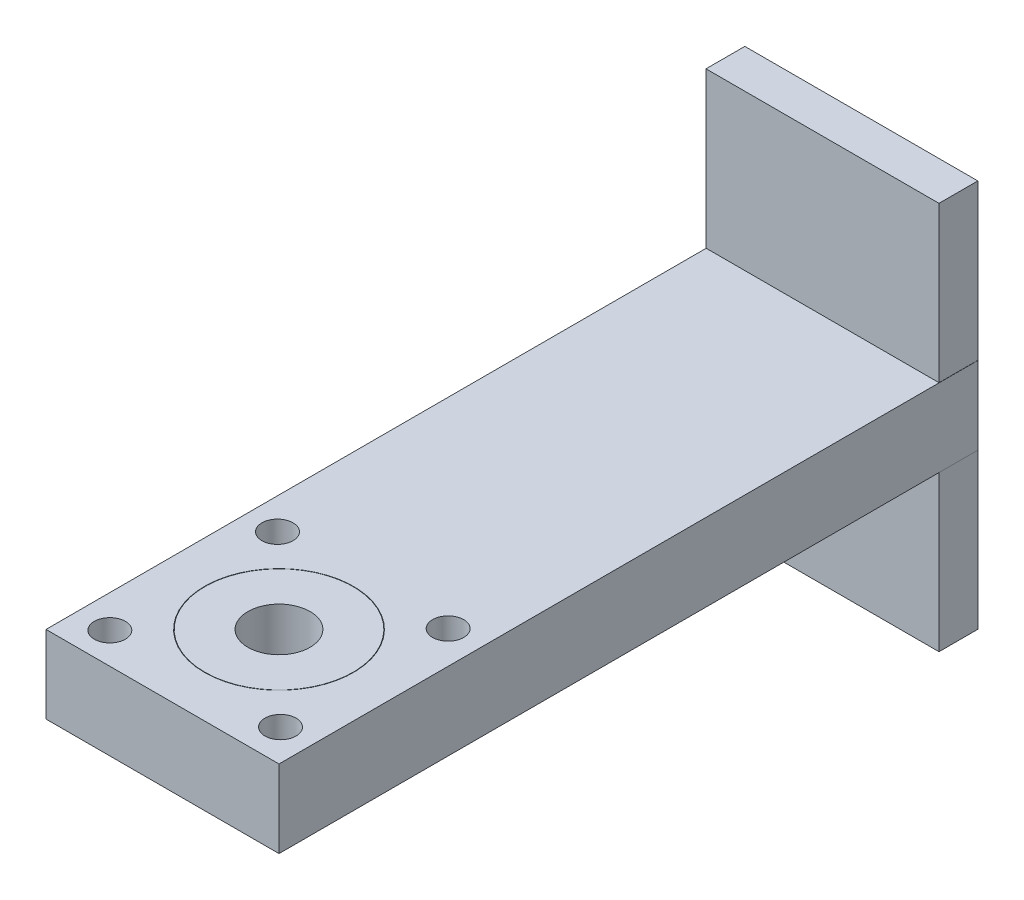
SolidWorks part; units mm, degrees
ref_plane "Front Plane" through (0, 0, 0) normal (0, 0, 1) x (1, 0, 0)
ref_plane "Top Plane" through (0, 0, 0) normal (0, 1, 0) x (1, 0, 0)
ref_plane "Right Plane" through (0, 0, 0) normal (1, 0, 0) x (0, 0, -1)
sketch "Sketch1" plane through (0, 0, 0) normal (0, 1, 0) x (1, 0, 0)
  line L1 (-15, 15) -> (15, 15)
  line L2 (-15, 15) -> (-15, -15)
  line L3 (-15, -15) -> (15, -15)
  line L4 (15, 15) -> (15, -15)
  line L5 (-15, 15) -> (15, -15) construction
  line L6 (-15, -15) -> (15, 15) construction
  point P0 (0, 0)
  dimension "D1" = 30
  dimension "D2" = 30
extrude "Boss-Extrude1" add sketch "Sketch1" along normal blind 10
sketch "Sketch2" plane through (0, 10, 0) normal (0, 1, 0) x (1, 0, 0)
  circle A0 centre (0, 0) radius 9.55
  circle A1 centre (0, 0) radius 9.6
extrude "Cut-Extrude1" cut sketch "Sketch2" against normal blind 7
sketch "Sketch3" plane through (0, 10, 0) normal (0, 1, 0) x (1, 0, 0)
  circle A0 centre (0, 0) radius 4
extrude "Cut-Extrude2" cut sketch "Sketch3" against normal blind 7
sketch "Sketch4" plane through (0, 10, 0) normal (0, 1, 0) x (1, 0, 0)
  circle A0 centre (10.7923, 10.9875) radius 2
extrude "Cut-Extrude3" cut sketch "Sketch4" against normal blind 10
pattern_circular "CirPattern1" count 4 every 90 about axis through (0, 0, 0) along (0, 1, 0) of "Cut-Extrude3"
sketch "Sketch5" plane through (0, 0, -15) normal (0, 0, -1) x (-1, 0, 0)
  line L1 (-15, 10) -> (15, 10)
  line L2 (-15, 10) -> (-15, 0)
  line L3 (-15, 0) -> (15, 0)
  line L4 (15, 10) -> (15, 0)
extrude "Boss-Extrude2" add sketch "Sketch5" along normal blind 60
sketch "Sketch6" plane through (0, 0, -75) normal (0, 0, -1) x (-1, 0, 0)
  line L1 (-14.977, -20) -> (15.023, -20)
  line L2 (-14.977, -20) -> (-14.977, 30)
  line L3 (-14.977, 30) -> (15.023, 30)
  line L4 (15.023, -20) -> (15.023, 30)
  line L5 (-14.977, -20) -> (15.023, 30) construction
  line L6 (-14.977, 30) -> (15.023, -20) construction
  line L9 (-15, 0) -> (15, 0) construction
  point P0 (0.023, 5)
  dimension "D1" = 15
  dimension "D2" = 50
  dimension "D3" = 5
extrude "Boss-Extrude3" add sketch "Sketch6" against normal blind 5
